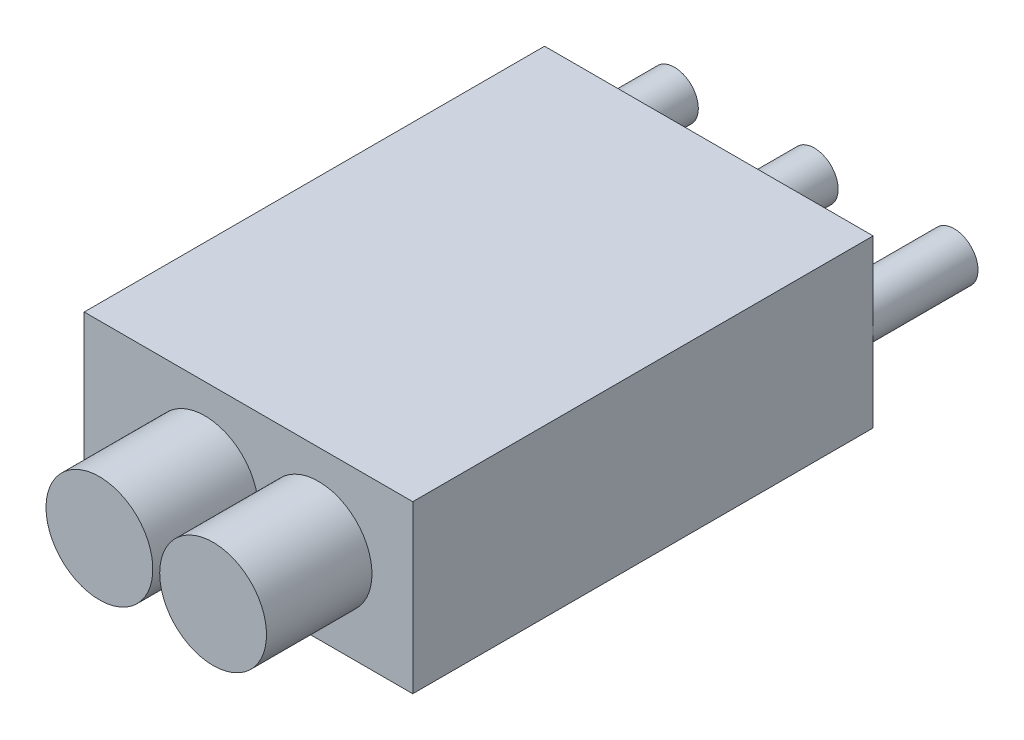
SolidWorks part; units mm, degrees
ref_plane "Front Plane" through (0, 0, 0) normal (0, 0, 1) x (1, 0, 0)
ref_plane "Top Plane" through (0, 0, 0) normal (0, 1, 0) x (1, 0, 0)
ref_plane "Right Plane" through (0, 0, 0) normal (1, 0, 0) x (0, 0, -1)
sketch "Sketch5" plane through (0, 0, 0) normal (0, 1, 0) x (1, 0, 0)
  line L2 (15.58, -21.83) -> (-15.58, -21.83)
  line L3 (15.58, -21.83) -> (15.58, 21.83)
  line L4 (15.58, 21.83) -> (-15.58, 21.83)
  line L5 (-15.58, -21.83) -> (-15.58, 21.83)
  line L6 (15.58, -21.83) -> (-15.58, 21.83) construction
  line L7 (15.58, 21.83) -> (-15.58, -21.83) construction
  point P2 (0, 0)
  dimension "D1" = 31.16
  dimension "D2" = 43.66
extrude "Boss-Extrude2" add sketch "Sketch5" along normal blind 15.78
sketch "Sketch6" plane through (0, 0, 0) normal (0, 0, 1) x (1, 0, 0)
  circle A0 centre (-4.1398, 7.9148) radius 5.065
  circle A1 centre (6.6434, 7.9148) radius 5.065
extrude "Boss-Extrude3" add sketch "Sketch6" along normal blind 10 from surface at 21.83 starting at face at (0, 7.89, 21.83)
sketch "Sketch7" plane through (0, 0, -21.83) normal (0, 0, -1) x (-1, 0, 0)
  circle A0 centre (-13.2621, 7.9496) radius 2.265
  circle A1 centre (0, 7.9496) radius 2.265
  circle A2 centre (13.2621, 7.9496) radius 2.265
  dimension "D1" = 4.53
extrude "Boss-Extrude4" add sketch "Sketch7" along normal blind 10
